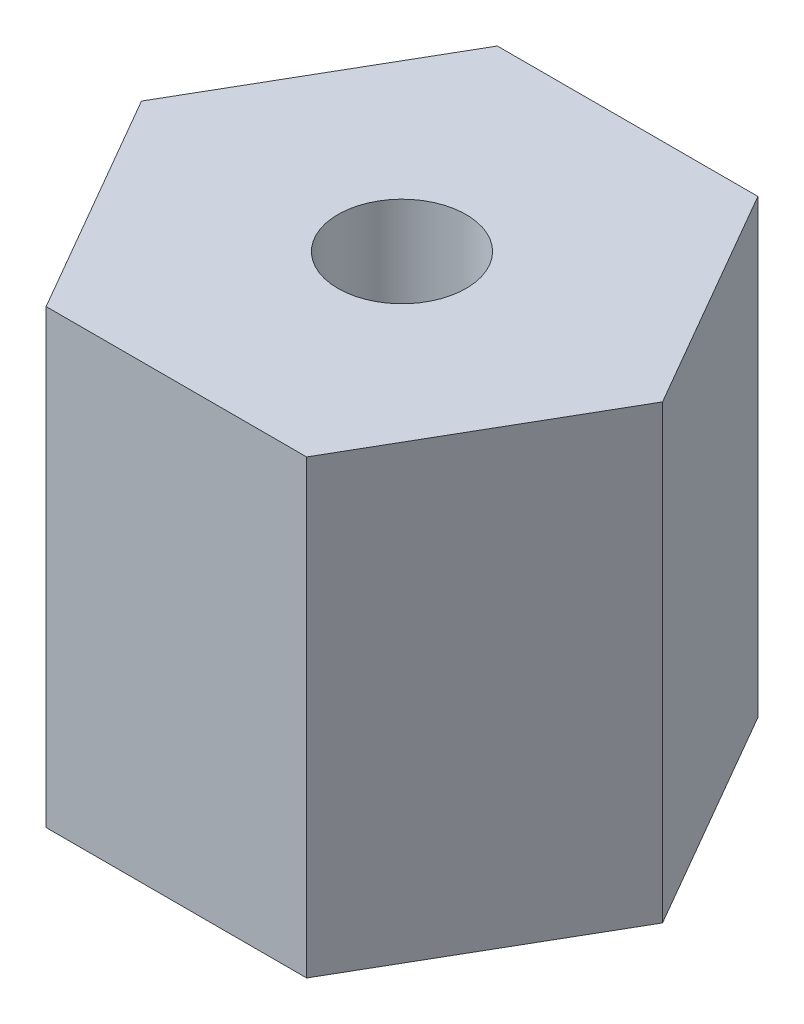
SolidWorks part; units mm, degrees
ref_plane "Front Plane" through (0, 0, 0) normal (0, 0, 1) x (1, 0, 0)
ref_plane "Top Plane" through (0, 0, 0) normal (0, 1, 0) x (1, 0, 0)
ref_plane "Right Plane" through (0, 0, 0) normal (1, 0, 0) x (0, 0, -1)
sketch "Sketch1" plane through (0, 0, 0) normal (0, 1, 0) x (1, 0, 0)
  line L1 (5.4993, 0) -> (2.7496, 4.7625)
  line L2 (2.7496, 4.7625) -> (-2.7496, 4.7625)
  line L3 (-2.7496, 4.7625) -> (-5.4993, 0)
  line L4 (-5.4993, 0) -> (-2.7496, -4.7625)
  line L5 (-2.7496, -4.7625) -> (2.7496, -4.7625)
  line L6 (2.7496, -4.7625) -> (5.4993, 0)
  circle A1 centre (0, 0) radius 4.7625 construction
  dimension "D1" = 9.525
extrude "Boss-Extrude1" add sketch "Sketch1" along normal blind 9.525
hole_wizard "#6-32 Tapped Hole1" positions "Sketch2" profile "Sketch3" tap size "#6-32" standard "ANSI Inch" end condition through all
sketch "Sketch2" plane through (0, 9.525, 0) normal (0, 1, 0) x (1, 0, 0)
  point P0 (0, 0)
sketch "Sketch3" plane through (0, 9.525, 0) normal (1, 0, 0) x (0, 0, 1)
  line L0 (0, 0) -> (0, 9.525)
  line L1 (0, 9.525) -> (1.3525, 9.525)
  line L2 (1.3525, 9.525) -> (1.3525, 0)
  line L5 (1.3525, 0) -> (0, 0)
  line L11 (0, -6.35) -> (0, 107.95) construction
  dimension "Thru Tap Drill Dia." = 2.7051
  dimension "Thru Tap Drill Depth" = 9.525
